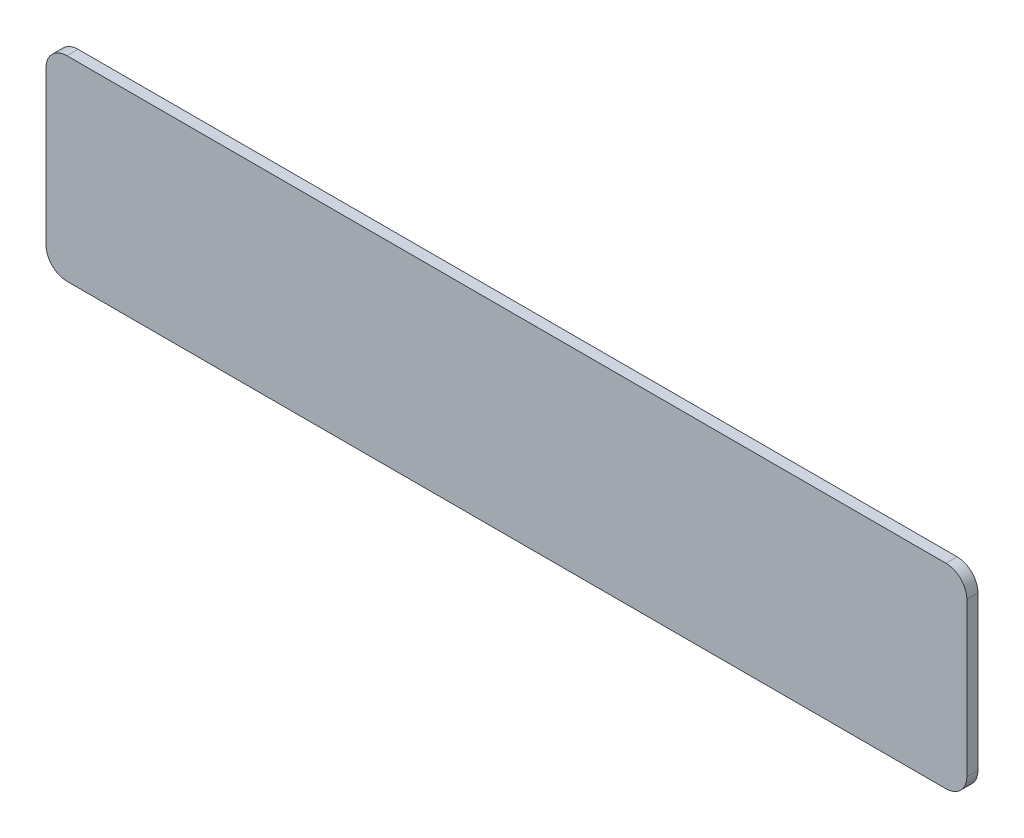
SolidWorks part; units mm, degrees
ref_plane "Front Plane" through (0, 0, 0) normal (0, 0, 1) x (1, 0, 0)
ref_plane "Top Plane" through (0, 0, 0) normal (0, 1, 0) x (1, 0, 0)
ref_plane "Right Plane" through (0, 0, 0) normal (1, 0, 0) x (0, 0, -1)
sketch "Sketch1" plane through (0, 0, 0) normal (0, 0, 1) x (1, 0, 0)
  line L1 (3, 0) -> (129, 0)
  line L2 (0, 3) -> (0, 25)
  line L3 (3, 28) -> (129, 28)
  line L4 (132, 3) -> (132, 25)
  arc A0 (129, 0) -> (132, 3) centre (129, 3) ccw
  arc A1 (129, 28) -> (132, 25) centre (129, 25) cw
  arc A2 (3, 0) -> (0, 3) centre (3, 3) cw
  arc A3 (0, 25) -> (3, 28) centre (3, 25) cw
  point P7 (132, 0)
  point P10 (132, 28)
  point P13 (0, 0)
  dimension "D3" = 3
  dimension "D1" = 132
  dimension "D2" = 28
extrude "Boss-Extrude1" add sketch "Sketch1" along normal blind 1.6
sketch "Sketch2" plane through (0, 0, 1.6) normal (0, 0, 1) x (1, 0, 0)
  line L0 (3, 0) -> (129, 0) construction
  line L1 (0, 25) -> (0, 3) construction
  point P0 (11, 9)
  point P1 (33, 9)
  point P2 (55, 9)
  point P3 (77, 9)
  point P4 (99, 9)
  dimension "D1" = 9
  dimension "D2" = 11
  dimension "D3" = 33
  dimension "D4" = 55
  dimension "D5" = 77
  dimension "D6" = 99
sketch "Sketch3" plane through (0, 0, 1.6) normal (0, 0, 1) x (1, 0, 0)
  line L0 (3, 0) -> (129, 0) construction
  line L1 (0, 25) -> (0, 3) construction
  point P0 (121, 9)
  dimension "D1" = 9
  dimension "D2" = 121
